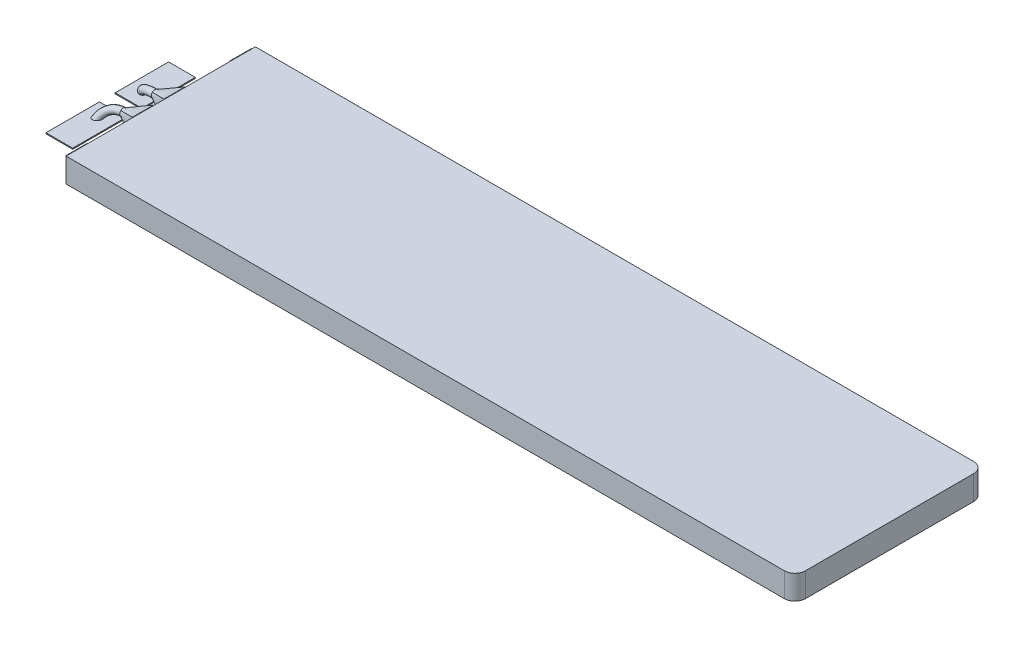
SolidWorks part; units mm, degrees
ref_plane "Front Plane" through (0, 0, 0) normal (0, 0, 1) x (1, 0, 0)
ref_plane "Top Plane" through (0, 0, 0) normal (0, 1, 0) x (1, 0, 0)
ref_plane "Right Plane" through (0, 0, 0) normal (1, 0, 0) x (0, 0, -1)
sketch "Sketch1" plane through (0, 0, 0) normal (0, 1, 0) x (1, 0, 0)
  line L0 (0, -55) -> (0, 55) construction
  line L1 (-34.65, 9) -> (33.65, 9)
  line L2 (-34.65, 9) -> (-34.65, -9)
  line L3 (-34.65, -9) -> (33.65, -9)
  line L4 (34.65, 8) -> (34.65, -8)
  line L5 (-55, 0) -> (55, 0) construction
  arc A0 (33.65, 9) -> (34.65, 8) centre (33.65, 8) cw
  arc A1 (33.65, -9) -> (34.65, -8) centre (33.65, -8) ccw
  point P10 (34.65, 9)
  point P13 (34.65, -9)
  dimension "D5" = 1
  dimension "D1" = 69.3
  dimension "D2" = 34.65
  dimension "D3" = 18
  dimension "D4" = 9
extrude "Boss-Extrude1" add sketch "Sketch1" along normal blind 2.3
sketch "Sketch2" plane through (-34.65, 0, 0) normal (-1, 0, 0) x (0, 0, 1)
  line L0 (0, -55) -> (0, 55) construction
  line L1 (-8.8, 2.15) -> (-6.8, 2.15)
  line L2 (-8.8, 2.15) -> (-8.8, 0.15)
  line L3 (-8.8, 0.15) -> (-6.8, 0.15)
  line L4 (-6.8, 2.15) -> (-6.8, 0.15)
  line L5 (-2.5, 2.15) -> (-0.5, 2.15)
  line L6 (-2.5, 2.15) -> (-2.5, 0.15)
  line L7 (-2.5, 0.15) -> (-0.5, 0.15)
  line L8 (-0.5, 2.15) -> (-0.5, 0.15)
  line L9 (0.5, 2.15) -> (2.5, 2.15)
  line L10 (0.5, 2.15) -> (0.5, 0.15)
  line L11 (0.5, 0.15) -> (2.5, 0.15)
  line L12 (2.5, 2.15) -> (2.5, 0.15)
  line L13 (6.8, 2.15) -> (8.8, 2.15)
  line L14 (6.8, 2.15) -> (6.8, 0.15)
  line L15 (6.8, 0.15) -> (8.8, 0.15)
  line L16 (8.8, 2.15) -> (8.8, 0.15)
  line L18 (55, 0) -> (-55, 0) construction
  dimension "D1" = 2
  dimension "D2" = 1
  dimension "D3" = 0.5
  dimension "D4" = 8.8
  dimension "D5" = 0.15
  dimension "D6" = 8.8
extrude "Boss-Extrude2" add sketch "Sketch2" along normal blind 0.2
sketch "Sketch3" plane through (-34.85, 0, 0) normal (-1, 0, 0) x (0, 0, 1)
  line L0 (-2.5, 2.15) -> (-0.5, 0.15)
sketch3d "3DSketch3"
  line L0 (-34.85, 1.15, -1.5) -> (-36.7096, 1.15, -1.5)
  line L1 (-34.85, 2.15, -2.5) -> (-34.85, 0.15, -0.5) construction
  line L2 (-38.66, -0.5, -2.54) -> (-38.66, -0.8696, -2.7729) construction
  arc A0 (-36.7096, 1.15, -1.5) -> (-38.66, -0.5, -2.54) centre (-36.7096, -0.5, -2.54) cw
  circle A1 centre (-36.7096, 1.15, -1.5) radius 0.34 construction
  point P5 (-36.7096, -1.54, -0.89)
  point P9 (-36.3696, 1.15, -1.5)
  dimension "D2" = 0.5
  dimension "D4" = 0.68
  dimension "D1" = 2.54
  dimension "D3" = 3.81
sketch "Sketch4" plane through (-34.85, 0, 0) normal (-1, 0, 0) x (0, 0, 1)
  circle A0 centre (-1.5, 1.15) radius 0.34
  circle A1 centre (-1.5, 1.15) radius 0.34 construction
ref_plane "Plane2" through (-36.7096, 1.15, -1.5) normal (-1, 0, 0) x (0, 0, 1)
sketch "Sketch5" plane through (-36.7096, 1.15, -1.5) normal (-1, 0, 0) x (0, 0, 1)
  circle A0 centre (0, 0) radius 0.34
  circle A1 centre (0, 0) radius 0.34 construction
sketch "Sketch6" plane through (-34.85, 0, 0) normal (-1, 0, 0) x (0, 0, 1)
  line L0 (-2.5, 0.15) -> (-0.5, 0.15) construction
  line L1 (-2.5, 2.15) -> (-0.5, 2.15)
  line L2 (-2.5, 2.15) -> (-2.5, 0.15)
  line L3 (-2.5, 0.15) -> (-0.5, 0.15)
  line L4 (-0.5, 2.15) -> (-0.5, 0.15)
loft "Loft1" add profiles "Sketch6", "Sketch5"
sweep "Sweep2" add profiles "Sketch4" path "3DSketch3"
mirror "Mirror4" about plane through (0, 0, 0) normal (0, 0, 1) of "Loft1", "Sweep2"
sketch "Sketch7" plane through (0, 0, 0) normal (0, 1, 0) x (1, 0, 0)
  line L0 (-1.265, 0) -> (1.265, 0) construction
  line L1 (-39.73, 5.83) -> (-37.19, 5.83)
  line L2 (-39.73, 5.83) -> (-39.73, 0.75)
  line L3 (-39.73, 0.75) -> (-37.19, 0.75)
  line L4 (-37.19, 5.83) -> (-37.19, 0.75)
  line L5 (-39.73, -0.75) -> (-37.19, -0.75)
  line L6 (-39.73, -0.75) -> (-39.73, -5.83)
  line L7 (-39.73, -5.83) -> (-37.19, -5.83)
  line L8 (-37.19, -0.75) -> (-37.19, -5.83)
  line L9 (-34.65, 9) -> (-34.65, -9) construction
  dimension "D1" = 5.08
  dimension "D2" = 2.54
  dimension "D3" = 1.5
  dimension "D4" = 0.75
  dimension "D5" = 2.54
  dimension "D6" = 5.08
extrude "Boss-Extrude3" add sketch "Sketch7" along normal blind 0.1
